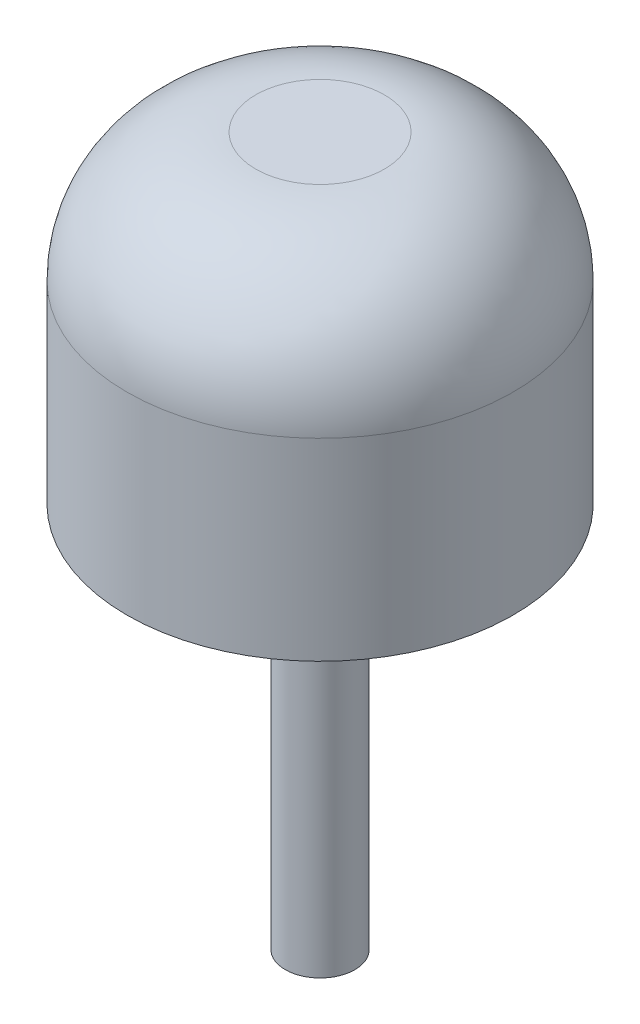
SolidWorks part; units mm, degrees
ref_plane "Front Plane" through (0, 0, 0) normal (0, 0, 1) x (1, 0, 0)
ref_plane "Top Plane" through (0, 0, 0) normal (0, 1, 0) x (1, 0, 0)
ref_plane "Right Plane" through (0, 0, 0) normal (1, 0, 0) x (0, 0, -1)
sketch "Sketch1" plane through (0, 0, 0) normal (0, 1, 0) x (1, 0, 0)
  circle A0 centre (0, 0) radius 3.81
extrude "Boss-Extrude1" add sketch "Sketch1" along normal blind 6.35
sketch "Sketch2" plane through (0, 0, 0) normal (0, -1, 0) x (1, 0, 0)
  circle A0 centre (0, 0) radius 0.6858
extrude "Boss-Extrude2" add sketch "Sketch2" along normal blind 7.62
fillet "Fillet1" radius 2.54 1 edges at (0, 6.35, 3.81)
